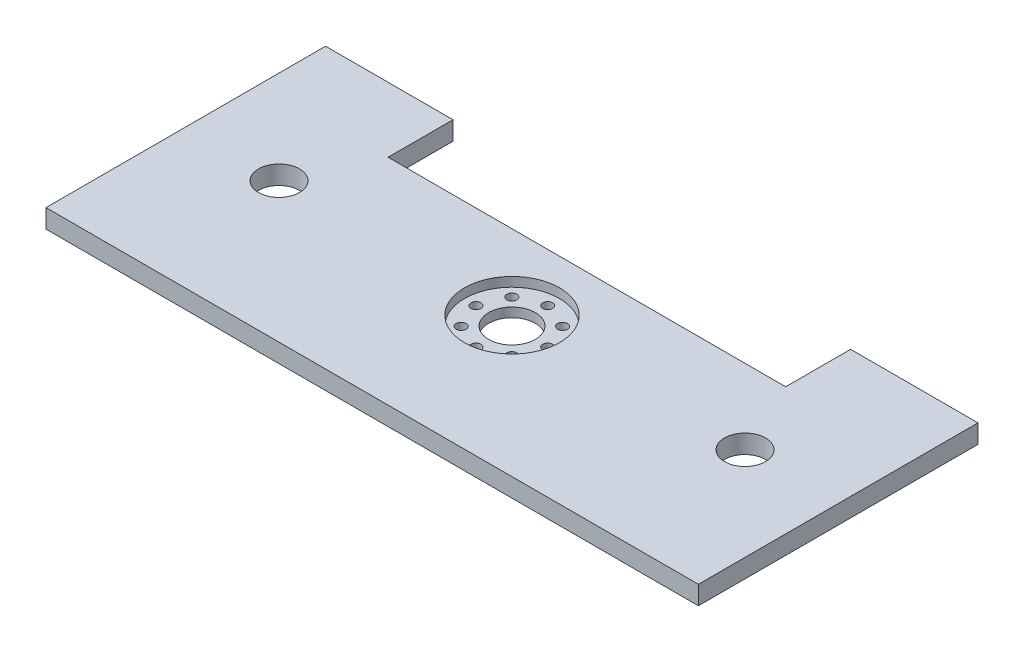
SolidWorks part; units mm, degrees
material "Pine"
ref_plane "Front Plane" through (0, 0, 0) normal (0, 0, 1) x (1, 0, 0)
ref_plane "Top Plane" through (0, 0, 0) normal (0, 1, 0) x (1, 0, 0)
ref_plane "Right Plane" through (0, 0, 0) normal (1, 0, 0) x (0, 0, -1)
sketch "Sketch1" plane through (0, 0, 0) normal (0, 1, 0) x (1, 0, 0)
  line L0 (-88.9, 0) -> (88.9, 0) construction
  line L1 (-88.9, 38.1) -> (88.9, 38.1)
  line L2 (-88.9, 38.1) -> (-88.9, -38.1)
  line L3 (-88.9, -38.1) -> (88.9, -38.1)
  line L4 (88.9, 38.1) -> (88.9, -38.1)
  line L5 (-88.9, 38.1) -> (88.9, -38.1) construction
  line L6 (-88.9, -38.1) -> (88.9, 38.1) construction
  line L7 (0, 0) -> (0, -38.1) construction
  line L8 (0, 0) -> (0, 38.1) construction
  circle A0 centre (-63.5, 0) radius 5.588
  circle A1 centre (63.5, 0) radius 5.588
  dimension "D4" = 11.176
  dimension "D1" = 177.8
  dimension "D2" = 76.2
extrude "Boss-Extrude1" add sketch "Sketch1" along normal blind 5.08
sketch "Sketch2" plane through (0, 5.08, 0) normal (0, 1, 0) x (1, 0, 0)
  line L0 (0, 0) -> (-63.5, 0) construction
  line L1 (0, 0) -> (63.5, 0) construction
  circle A0 centre (0, 0) radius 12.954
  circle A1 centre (6.9805, -7.023) radius 0.7121
  circle A2 centre (9.8447, -0.1082) radius 0.7121
  circle A3 centre (-6.8491, -7.023) radius 0.7121
  circle A4 centre (0.0657, -9.8872) radius 0.7121
  circle A5 centre (6.9805, 6.8065) radius 0.7121
  circle A6 centre (0.0657, 9.6708) radius 0.7121
  circle A7 centre (-6.8491, 6.8065) radius 0.7121
  circle A8 centre (-9.7133, -0.1082) radius 0.7121
  point P3 (0.0657, -9.8872)
  point P8 (-6.8491, -7.023)
  point P9 (-9.7133, -0.1082)
  point P10 (-6.8491, 6.8065)
  point P11 (0.0657, 9.6708)
  point P12 (6.9805, 6.8065)
  point P13 (9.8447, -0.1082)
  point P14 (6.9805, -7.023)
extrude "Cut-Extrude1" cut sketch "Sketch2" against normal blind 2.54
sketch "Sketch4" plane through (0, 5.08, 0) normal (0, 1, 0) x (1, 0, 0)
  circle A0 centre (0, 0) radius 6.35
extrude "Cut-Extrude2" cut sketch "Sketch4" against normal through all
hole_wizard "#6-32 Tapped Hole2" positions "Sketch7" profile "Sketch6" tap size "#6-32" standard "ANSI Inch" end condition through all
sketch "Sketch7" plane through (0, 2.54, 0) normal (0, 1, 0) x (1, 0, 0)
  point P0 (6.9805, 6.8065)
  point P3 (9.8447, -0.1082)
  point P6 (6.9805, -7.023)
  point P9 (0.0657, 9.6708)
  point P12 (-6.8491, 6.8065)
  point P15 (-9.7133, -0.1082)
  point P18 (-6.8491, -7.023)
  point P21 (0.0657, -9.8872)
sketch "Sketch6" plane through (6.9805, 2.54, -6.8065) normal (1, 0, 0) x (0, 0, 1)
  line L0 (0, 0) -> (0, 2.54)
  line L1 (0, 2.54) -> (1.3525, 2.54)
  line L2 (1.3525, 2.54) -> (1.3525, 0)
  line L5 (1.3525, 0) -> (0, 0)
  line L11 (0, -6.35) -> (0, 107.95) construction
  dimension "Thread Major Dia." = 2.7051
  dimension "Thru Tap Drill Depth" = 2.54
sketch "Sketch9" plane through (0, 0, 0) normal (0, 1, 0) x (1, 0, 0)
  line L0 (88.9, 38.1) -> (-88.9, 38.1) construction
  line L1 (54.1798, 20.4086) -> (-54.1798, 20.4086)
  line L2 (54.1798, 20.4086) -> (54.1798, 38.1)
  line L3 (54.1798, 38.1) -> (-54.1798, 38.1)
  line L4 (-54.1798, 20.4086) -> (-54.1798, 38.1)
  line L5 (54.1798, 20.4086) -> (-54.1798, 38.1) construction
  line L6 (54.1798, 38.1) -> (-54.1798, 20.4086) construction
  point P0 (0, 29.2543)
extrude "Cut-Extrude7" cut sketch "Sketch9" along normal blind 5.08
